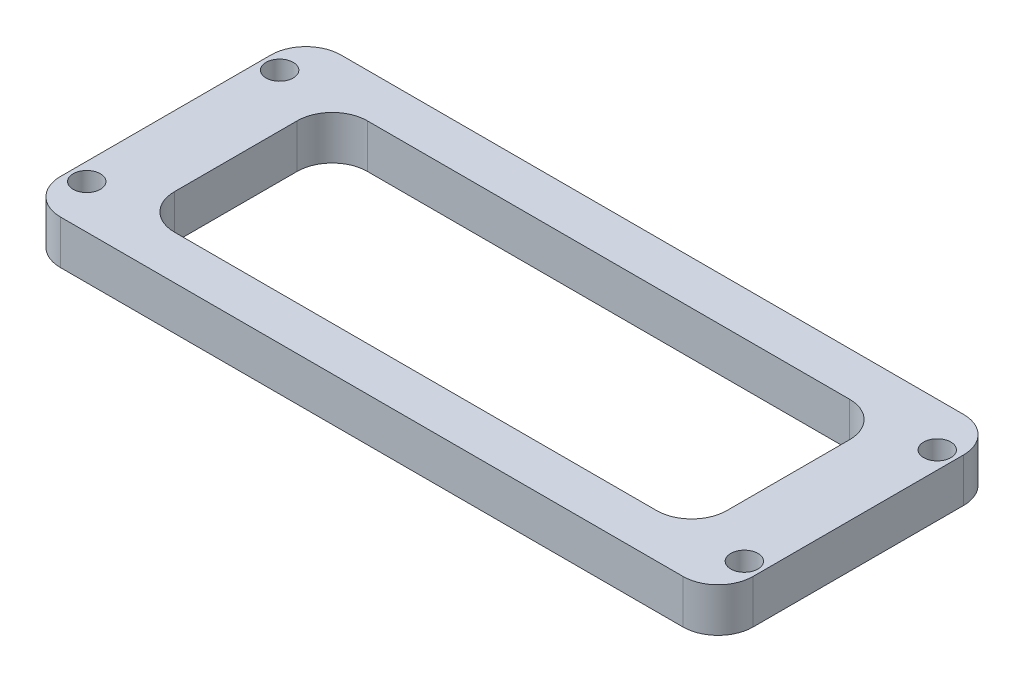
SolidWorks part; units mm, degrees
ref_plane "前视基准面" through (0, 0, 0) normal (0, 0, 1) x (1, 0, 0)
ref_plane "上视基准面" through (0, 0, 0) normal (0, 1, 0) x (1, 0, 0)
ref_plane "右视基准面" through (0, 0, 0) normal (1, 0, 0) x (0, 0, -1)
sketch "草图1" plane through (0, 0, 0) normal (0, 1, 0) x (1, 0, 0)
  line L1 (-37.5, 11) -> (37.5, 11) construction
  line L2 (-37.5, 11) -> (-37.5, -11) construction
  line L3 (-37.5, -11) -> (37.5, -11) construction
  line L4 (37.5, 11) -> (37.5, -11) construction
  line L5 (-37.5, 11) -> (37.5, -11) construction
  line L6 (-37.5, -11) -> (37.5, 11) construction
  line L11 (-39.5, 16) -> (39.5, 16)
  line L12 (-39.5, 16) -> (-39.5, -16)
  line L13 (-39.5, -16) -> (39.5, -16)
  line L14 (39.5, 16) -> (39.5, -16)
  line L15 (-39.5, 16) -> (39.5, -16) construction
  line L16 (-39.5, -16) -> (39.5, 16) construction
  circle A0 centre (-37.5, 11) radius 1.55
  circle A1 centre (-37.5, -11) radius 1.55
  circle A2 centre (37.5, 11) radius 1.55
  circle A3 centre (37.5, -11) radius 1.55
  point P0 (0, 0)
  point P6 (0, 0)
  point P7 (0, 0)
  dimension "D3" = 3.1
  dimension "D1" = 75
  dimension "D2" = 22
  dimension "D4" = 79
  dimension "D5" = 32
extrude "凸台-拉伸1" add sketch "草图1" along normal blind 5
fillet "圆角1" radius 4 4 edges at (-39.5, 2.5, 16) (-39.5, 2.5, -16) (39.5, 2.5, -16) (39.5, 2.5, 16)
sketch "草图2" plane through (0, 5, 0) normal (0, 1, 0) x (1, 0, 0)
  line L0 (39.5, -12) -> (39.5, 12) construction
  line L1 (-31.5, 11) -> (31.5, 11)
  line L2 (-31.5, 11) -> (-31.5, -11)
  line L3 (-31.5, -11) -> (31.5, -11)
  line L4 (31.5, 11) -> (31.5, -11)
  line L5 (-31.5, 11) -> (31.5, -11) construction
  line L6 (-31.5, -11) -> (31.5, 11) construction
  line L7 (35.5, 16) -> (-35.5, 16) construction
  point P0 (0, 0)
  dimension "D1" = 8
  dimension "D2" = 5
extrude "切除-拉伸1" cut sketch "草图2" against normal through all
fillet "圆角2" radius 4 4 edges at (-31.5, 2.5, 11) (31.5, 2.5, -11) (31.5, 2.5, 11) (-31.5, 2.5, -11)
